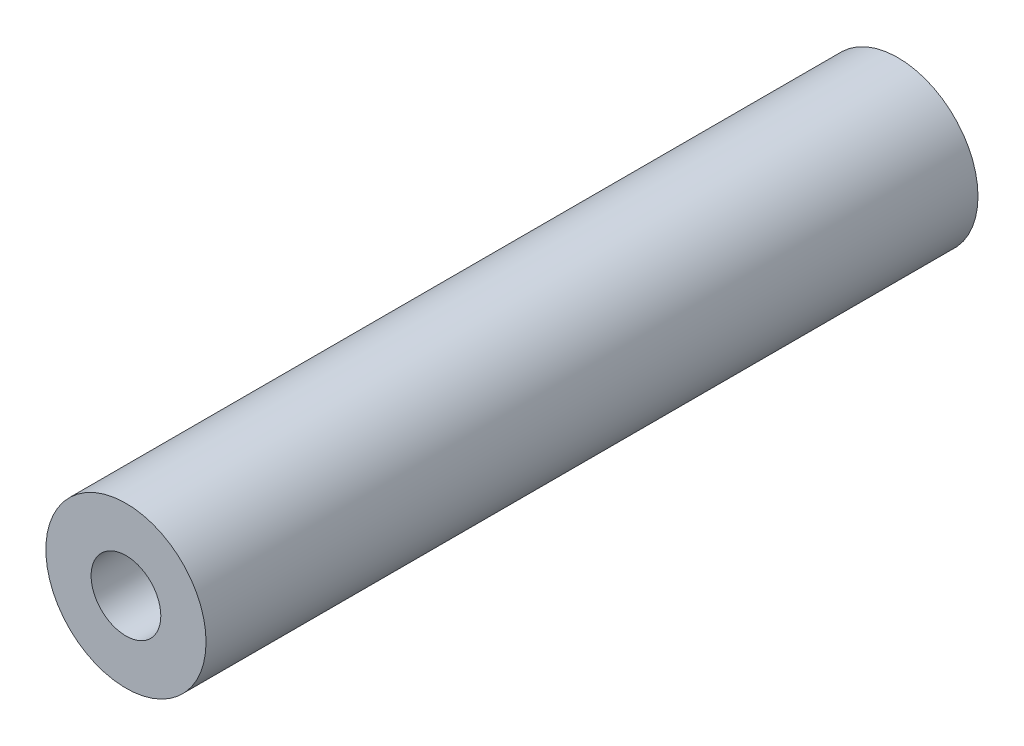
SolidWorks part; units mm, degrees
ref_plane "Front Plane" through (0, 0, 0) normal (0, 0, 1) x (1, 0, 0)
ref_plane "Top Plane" through (0, 0, 0) normal (0, 1, 0) x (1, 0, 0)
ref_plane "Right Plane" through (0, 0, 0) normal (1, 0, 0) x (0, 0, -1)
sketch "Sketch1" plane through (0, 0, 0) normal (0, 0, 1) x (1, 0, 0)
  circle A0 centre (0, 0) radius 13.49
  circle A1 centre (0, 0) radius 5.87
  dimension "D1" = 26.98
  dimension "D2" = 7.62
extrude "Boss-Extrude1" add sketch "Sketch1" along normal blind 130
